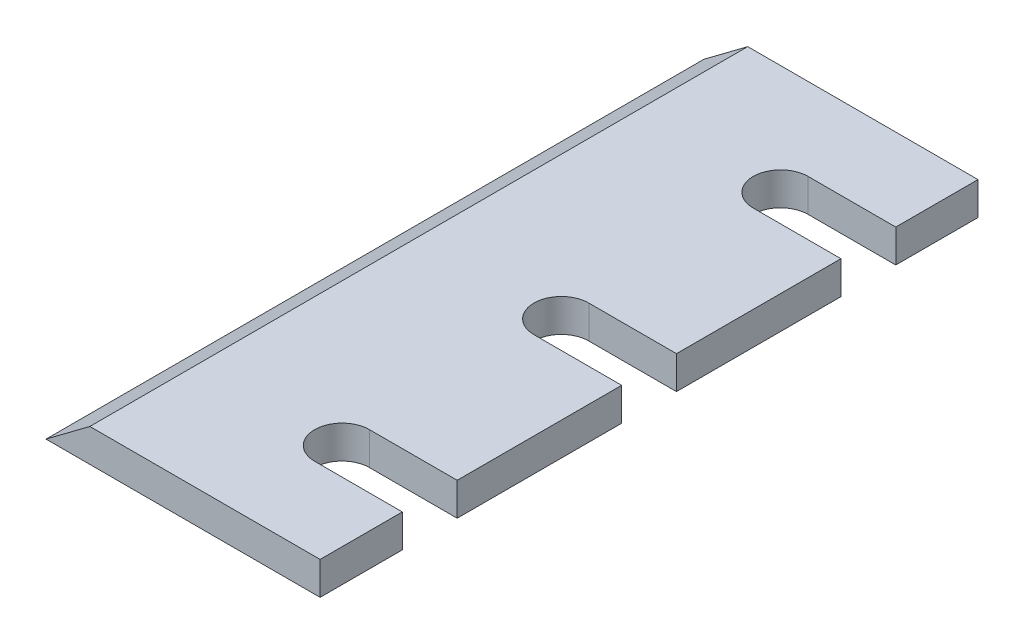
SolidWorks part; units mm, degrees
ref_plane "Ebene vorne" through (0, 0, 0) normal (0, 0, 1) x (1, 0, 0)
ref_plane "Ebene oben" through (0, 0, 0) normal (0, 1, 0) x (1, 0, 0)
ref_plane "Ebene rechts" through (0, 0, 0) normal (1, 0, 0) x (0, 0, -1)
sketch "Skizze1" plane through (0, 0, 0) normal (0, 0, 1) x (1, 0, 0)
  line L0 (0, 0) -> (25, 0)
  line L1 (25, 0) -> (25, 3)
  line L2 (25, 3) -> (4, 3)
  line L3 (4, 3) -> (0, 0)
  dimension "D1" = 25
  dimension "D2" = 3
  dimension "D3" = 21
extrude "Aufsatz-Linear austragen1" add sketch "Skizze1" along normal blind 60
sketch "Skizze2" plane through (0, 3, 0) normal (0, 1, 0) x (1, 0, 0)
  line L0 (25, -52.5) -> (17, -52.5)
  line L1 (25, -60) -> (25, 0) construction
  line L2 (25, -47.5) -> (17, -47.5)
  line L4 (25, -60) -> (4, -60) construction
  line L5 (25, -32.5) -> (17, -32.5)
  line L6 (25, -27.5) -> (17, -27.5)
  line L7 (25, -12.5) -> (17, -12.5)
  line L8 (25, -7.5) -> (17, -7.5)
  line L9 (25, 0) -> (4, 0) construction
  line L10 (25, -52.5) -> (25, -47.5)
  line L11 (25, -32.5) -> (25, -27.5)
  line L12 (25, -12.5) -> (25, -7.5)
  arc A0 (17, -52.5) -> (17, -47.5) centre (17, -50) cw
  arc A1 (17, -32.5) -> (17, -27.5) centre (17, -30) cw
  arc A2 (17, -12.5) -> (17, -7.5) centre (17, -10) cw
  point P19 (14.5, 0)
  dimension "D8" = 8
  dimension "D1" = 5
  dimension "D2" = 8
  dimension "D3" = 10
  dimension "D4" = 5
  dimension "D5" = 5
  dimension "D6" = 8
  dimension "D7" = 30
  dimension "D9" = 10
  dimension "D10" = 8
  dimension "D11" = 8
extrude "Schnitt-Linear austragen1" cut sketch "Skizze2" against normal through all
